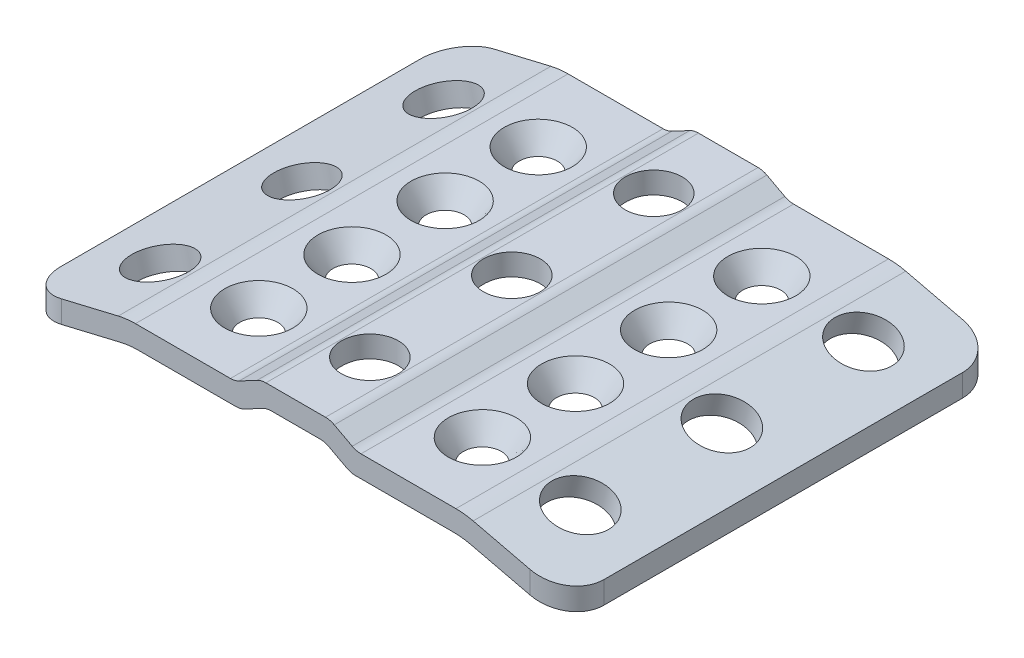
SolidWorks part; units mm, degrees
material "6063-T6"
ref_plane "Front Plane" through (0, 0, 0) normal (0, 0, 1) x (1, 0, 0)
ref_plane "Top Plane" through (0, 0, 0) normal (0, 1, 0) x (1, 0, 0)
ref_plane "Right Plane" through (0, 0, 0) normal (1, 0, 0) x (0, 0, -1)
sketch "Sketch1" plane through (0, 0, 0) normal (0, 0, 1) x (1, 0, 0)
  line L0 (0, 0) -> (3.3274, 0)
  line L1 (4.5227, -0.2988) -> (6.9656, -1.6017)
  line L2 (8.1609, -1.9005) -> (21.4986, -1.9005)
  line L3 (23.8485, -2.176) -> (36.9899, -5.3001)
  line L5 (-4.064, 2.9464) -> (4.064, 2.9464)
  line L6 (5.2593, 2.6476) -> (7.7022, 1.3447)
  line L7 (8.8975, 1.0459) -> (21.844, 1.0459)
  line L8 (24.1939, 0.7704) -> (36.9899, -2.2716)
  line L9 (36.9899, -2.2716) -> (36.9899, -5.3001)
  line L10 (0, 2.9464) -> (0, 23.1998) construction
  line L11 (-36.9899, -2.2716) -> (-36.9899, -5.3001)
  line L12 (-24.1939, 0.7704) -> (-36.9899, -2.2716)
  line L13 (-8.8975, 1.0459) -> (-21.844, 1.0459)
  line L14 (-5.2593, 2.6476) -> (-7.7022, 1.3447)
  line L15 (-23.8485, -2.176) -> (-36.9899, -5.3001)
  line L16 (-8.1609, -1.9005) -> (-21.4986, -1.9005)
  line L17 (-4.5227, -0.2988) -> (-6.9656, -1.6017)
  line L18 (0, 0) -> (-3.3274, 0)
  arc A0 (6.9656, -1.6017) -> (8.1609, -1.9005) centre (8.1609, 0.6395) ccw
  arc A1 (7.7022, 1.3447) -> (8.8975, 1.0459) centre (8.8975, 3.5859) ccw
  arc A2 (3.3274, 0) -> (4.5227, -0.2988) centre (3.3274, -2.54) cw
  arc A3 (4.064, 2.9464) -> (5.2593, 2.6476) centre (4.064, 0.4064) cw
  arc A4 (21.4986, -1.9005) -> (23.8485, -2.176) centre (21.4986, -12.0605) cw
  arc A5 (21.844, 1.0459) -> (24.1939, 0.7704) centre (21.844, -9.1141) cw
  arc A6 (-21.844, 1.0459) -> (-24.1939, 0.7704) centre (-21.844, -9.1141) ccw
  arc A7 (-21.4986, -1.9005) -> (-23.8485, -2.176) centre (-21.4986, -12.0605) ccw
  arc A8 (-4.064, 2.9464) -> (-5.2593, 2.6476) centre (-4.064, 0.4064) ccw
  arc A9 (-3.3274, 0) -> (-4.5227, -0.2988) centre (-3.3274, -2.54) ccw
  arc A10 (-7.7022, 1.3447) -> (-8.8975, 1.0459) centre (-8.8975, 3.5859) cw
  arc A11 (-6.9656, -1.6017) -> (-8.1609, -1.9005) centre (-8.1609, 0.6395) cw
  point P13 (7.5259, -1.9005)
  point P18 (3.9624, 0)
  point P23 (22.6897, -1.9005)
  point P26 (1.6637, 0)
  point P48 (-22.6897, -1.9005)
  point P49 (-3.9624, 0)
  point P50 (-7.5259, -1.9005)
  dimension "D5" = 2.54
  dimension "D6" = 10.16
  dimension "D7" = 2.9464
  dimension "D11" = 12.9465
  dimension "D13" = 4.064
  dimension "D1" = 3.9624
  dimension "D2" = 4.0386
  dimension "D3" = 15.1638
  dimension "D4" = 14.3002
  dimension "D8" = 2.9464
  dimension "D9" = 2.9464
  dimension "D10" = 2.9464
  dimension "D12" = 13.3377
extrude "Boss-Extrude1" add sketch "Sketch1" along normal blind 58.9788
fillet "Fillet3" radius 5.0292 4 edges at (-36.9899, -3.7859, 0) (-36.9899, -3.7859, 58.9788) (36.9899, -3.7859, 0) (36.9899, -3.7859, 58.9788)
sketch "Sketch2" plane through (-1.4676, 6.1732, 0) normal (-0.2313, 0.9729, 0) x (0.9729, 0.2313, 0)
  line L1 (-36.5123, -53.9496) -> (-36.5123, -5.0292) construction
  line L3 (-23.3597, -58.9788) -> (-31.3429, -58.9788) construction
  circle A0 centre (-27.9271, -10.1854) radius 3.9878
  circle A1 centre (-27.9271, -29.4894) radius 3.937
  circle A2 centre (-27.9271, -48.8188) radius 3.9878
  dimension "D1" = 7.9756
  dimension "D2" = 8.5852
  dimension "D3" = 29.4894
  dimension "D4" = 7.874
  dimension "D5" = 7.9756
  dimension "D6" = 19.304
  dimension "D7" = 8.5852
  dimension "D8" = 8.5852
  dimension "D9" = 10.16
extrude "Cut-Extrude1" cut sketch "Sketch2" against normal blind 58.9788
sketch "Sketch3" plane through (0, 1.0459, 0) normal (0, 1, 0) x (1, 0, 0)
  line L0 (-8.8975, 0) -> (-21.844, 0) construction
  line L2 (-15.24, -10.668) -> (-15.24, -48.768) construction
  circle A0 centre (-15.24, -10.668) radius 4.6482
  circle A1 centre (-15.24, -23.368) radius 4.6482
  circle A2 centre (-15.24, -36.068) radius 4.6482
  circle A3 centre (-15.24, -48.768) radius 4.6482
  dimension "D1" = 9.2964
  dimension "D2" = 10.668
  dimension "D3" = 15.24
  dimension "D4" = 4
  dimension "D5" = 12.7
extrude "Cut-Extrude6" cut sketch "Sketch3" against normal blind 3.0988 draft 35
sketch "Sketch5" plane through (0, 1.0459, 0) normal (0, 1, 0) x (1, 0, 0)
  line L0 (21.844, 0) -> (8.8975, 0) construction
  line L2 (15.24, -10.668) -> (15.24, -48.768) construction
  circle A0 centre (15.24, -10.668) radius 4.6482
  circle A1 centre (15.24, -23.368) radius 4.6482
  circle A2 centre (15.24, -36.068) radius 4.6482
  circle A3 centre (15.24, -48.768) radius 4.6482
  dimension "D1" = 9.2964
  dimension "D2" = 10.668
  dimension "D3" = 15.24
  dimension "D5" = 12.7
  dimension "D4" = 4
extrude "Cut-Extrude7" cut sketch "Sketch5" against normal blind 3.0988 draft 35
sketch "Sketch6" plane through (1.4676, 6.1732, 0) normal (0.2313, 0.9729, 0) x (0.9729, -0.2313, 0)
  line L0 (31.3429, 0) -> (23.3597, 0) construction
  line L1 (36.5123, -53.9496) -> (36.5123, -5.0292) construction
  line L2 (27.8763, -10.16) -> (27.8763, -48.768) construction
  circle A0 centre (27.8763, -10.16) radius 3.9878
  circle A1 centre (27.8763, -29.464) radius 3.9878
  circle A2 centre (27.8763, -48.768) radius 3.9878
  dimension "D1" = 7.9756
  dimension "D2" = 10.16
  dimension "D3" = 8.636
  dimension "D5" = 19.304
  dimension "D4" = 3
extrude "Cut-Extrude8" cut sketch "Sketch6" against normal blind 50.8
sketch "Sketch7" plane through (0, 2.9464, 0) normal (0, 1, 0) x (1, 0, 0)
  line L0 (0, -10.16) -> (0, -48.8696) construction
  line L2 (-4.064, -58.9788) -> (-4.064, 0) construction
  line L3 (4.064, 0) -> (-4.064, 0) construction
  circle A0 centre (0, -10.16) radius 3.8862
  circle A1 centre (0, -29.5148) radius 3.8862
  circle A2 centre (0, -48.8696) radius 3.8862
  dimension "D1" = 7.7724
  dimension "D2" = 4.064
  dimension "D3" = 10.16
  dimension "D5" = 19.3548
  dimension "D4" = 3
extrude "Cut-Extrude9" cut sketch "Sketch7" against normal blind 50.8
